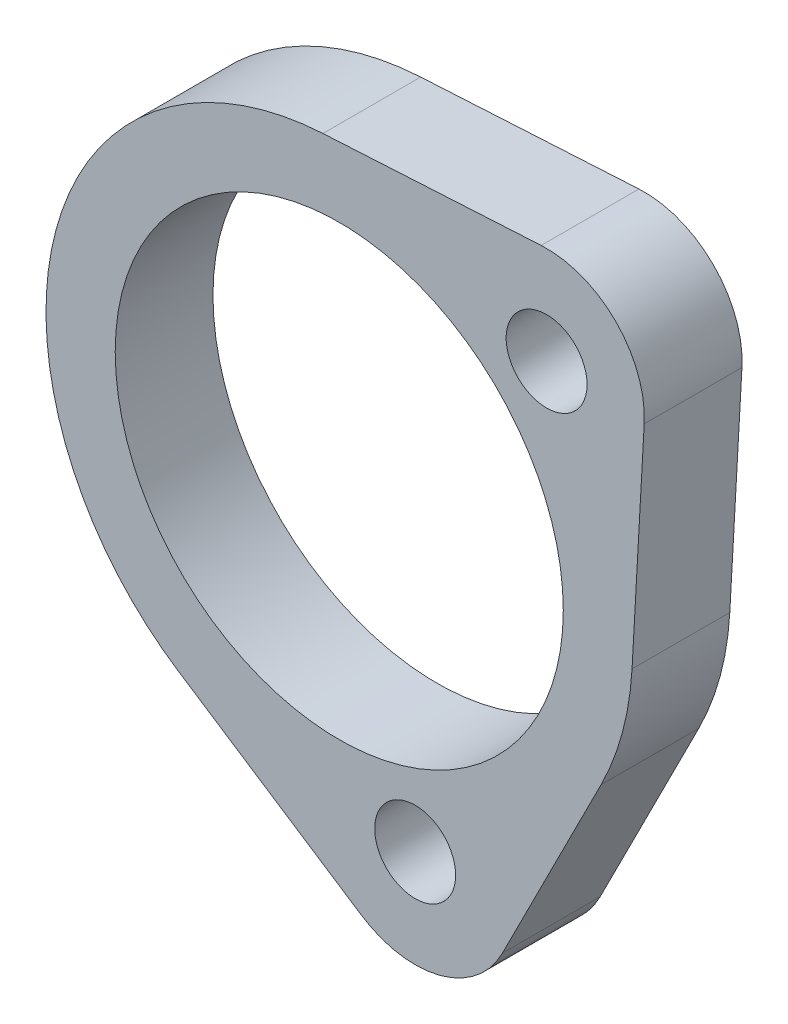
SolidWorks part; units mm, degrees
material "6061-T6 (SS)"
ref_plane "Front Plane" through (0, 0, 0) normal (0, 0, 1) x (1, 0, 0)
ref_plane "Top Plane" through (0, 0, 0) normal (0, 1, 0) x (1, 0, 0)
ref_plane "Right Plane" through (0, 0, 0) normal (1, 0, 0) x (0, 0, -1)
sketch "Sketch1" plane through (0, 0, 0) normal (0, 0, 1) x (1, 0, 0)
  line L0 (0, 0) -> (13.4704, 13.4704) construction
  line L1 (0, 0) -> (4.9305, -18.4009) construction
  line L2 (0, 0) -> (-18.3341, -18.3341) construction
  line L3 (0, 0) -> (-25.3324, 0) construction
  line L4 (-10.4282, -15.9422) -> (1.4544, -23.715)
  line L6 (-1.06, 19.0205) -> (13.1171, 19.8105)
  line L7 (19.0205, -1.06) -> (19.8105, 13.1171)
  line L8 (10.5979, -21.265) -> (17.0022, -8.5923)
  circle A0 centre (0, 0) radius 14.5542
  circle A1 centre (4.9305, -18.4009) radius 2.6289
  circle A2 centre (13.4704, 13.4704) radius 2.6289
  arc A3 (19.8105, 13.1171) -> (13.1171, 19.8105) centre (13.4704, 13.4704) ccw
  arc A4 (-1.06, 19.0205) -> (-10.4282, -15.9422) centre (0, 0) ccw
  arc A5 (10.5979, -21.265) -> (1.4544, -23.715) centre (4.9305, -18.4009) cw
  arc A6 (17.0022, -8.5923) -> (19.0205, -1.06) centre (0, 0) ccw
  point P15 (18.7652, -8.5031)
  point P19 (2.4653, 1.3497)
  dimension "D1" = 29.1084
  dimension "D4" = 5.2578
  dimension "D5" = 5.2578
  dimension "D8" = 6.35
  dimension "D9" = 19.05
  dimension "D10" = 6.35
  dimension "D11" = 19.05
  dimension "D2" = 45
  dimension "D3" = 60
  dimension "D6" = 19.05
  dimension "D7" = 19.05
extrude "Boss-Extrude1" add sketch "Sketch1" along normal blind 6.35
